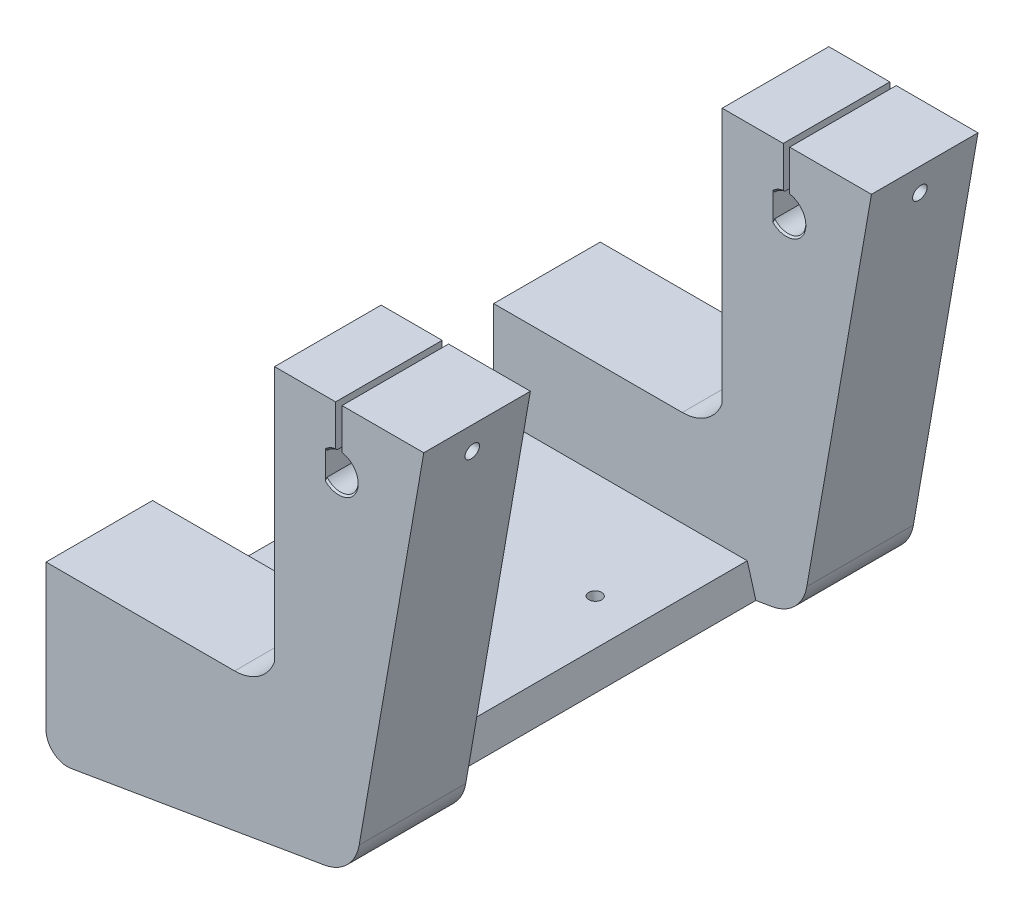
SolidWorks part; units mm, degrees
material "PLA"
ref_plane "Front Plane" through (0, 0, 0) normal (0, 0, 1) x (1, 0, 0)
ref_plane "Top Plane" through (0, 0, 0) normal (0, 1, 0) x (1, 0, 0)
ref_plane "Right Plane" through (0, 0, 0) normal (1, 0, 0) x (0, 0, -1)
sketch "Sketch1" plane through (0, 0, 0) normal (0, 0, 1) x (1, 0, 0)
  line L1 (0, 0) -> (0, -25.5549)
  line L2 (0, 0) -> (0, 36) construction
  line L3 (0, 36) -> (-73.6122, -6.5) construction
  line L4 (-73.6122, -6.5) -> (-73.6122, -40.5794)
  line L5 (-67.7751, -45.5088) -> (-8.3259, -35.4138)
  line L6 (-73.6122, -6.5) -> (-29.3679, -6.5)
  line L7 (-19.971, 0.0798) -> (-20, 0)
  line L8 (-20, 0) -> (0, 0)
  arc A0 (0, -25.5549) -> (-8.3259, -35.4138) centre (-10, -25.5549) cw
  arc A1 (-29.3679, -6.5) -> (-19.971, 0.0798) centre (-29.3679, 3.5) ccw
  arc A2 (-67.7751, -45.5088) -> (-73.6122, -40.5794) centre (-68.6122, -40.5794) cw
  point P10 (0, -34)
  point P15 (-73.6122, -46.5)
  dimension "D8" = 10
  dimension "D9" = 10
  dimension "D10" = 5
  dimension "D1" = 36
  dimension "D2" = 70
  dimension "D3" = 60
  dimension "D4" = 40
  dimension "D5" = 85
  dimension "D6" = 110
  dimension "D7" = 20
extrude "Boss-Extrude1" add sketch "Sketch1" along normal mid plane 130
sketch "Sketch2" plane through (0, 0, 0) normal (0, 0, 1) x (1, 0, 0)
  line L0 (-20, 0) -> (-19.971, 0.0798) construction
  line L1 (0, -25.5549) -> (0, 0) construction
  line L2 (0, 0) -> (-20, 0) construction
  line L3 (-20, 0) -> (-19.971, 0.0798)
  line L4 (0, -25.5549) -> (0, 0)
  line L5 (0, 0) -> (-20, 0)
  line L6 (-21.617, -2.8185) -> (-12.1021, -36.055)
  line L7 (-67.7751, -45.5088) -> (-8.3259, -35.4138) construction
  line L8 (-12.1021, -36.055) -> (-8.3259, -35.4138)
  arc A0 (-29.3679, -6.5) -> (-19.971, 0.0798) centre (-29.3679, 3.5) ccw construction
  arc A1 (-8.3259, -35.4138) -> (0, -25.5549) centre (-10, -25.5549) ccw construction
  arc A2 (-21.617, -2.8185) -> (-19.971, 0.0798) centre (-29.3679, 3.5) ccw
  arc A3 (-8.3259, -35.4138) -> (0, -25.5549) centre (-10, -25.5549) ccw
extrude "Cut-Extrude1" cut sketch "Sketch2" against normal mid plane 80
sketch "Sketch5" plane through (0, -6.5, 0) normal (0, 1, 0) x (1, 0, 0)
  line L0 (-73.6122, -65) -> (-73.6122, 65) construction
  line L1 (-73.6122, 40) -> (-29.4017, 40)
  line L2 (-73.6122, 40) -> (-73.6122, -40)
  line L3 (-73.6122, -40) -> (-29.3679, -40)
  line L5 (-29.3679, -65) -> (-29.3679, 65) construction
  line L6 (-29.3679, 65) -> (-73.6122, 65) construction
  line L7 (-29.3679, -65) -> (-73.6122, -65) construction
  line L8 (-29.3679, -40) -> (0, -40)
  line L9 (0, -40) -> (0, 40)
  line L10 (0, 40) -> (-29.4017, 40)
  dimension "D1" = 25
  dimension "D2" = 25
extrude "Cut-Extrude4" cut sketch "Sketch5" against normal mid plane 45
sketch "Sketch11" plane through (0, 0, 0) normal (0, 1, 0) x (1, 0, 0)
  line L4 (0, 40) -> (0, 65)
  line L5 (0, 65) -> (-20, 65)
  line L6 (0, 40) -> (0, 65)
  line L7 (-20, 40) -> (0, 40)
  line L9 (0, 65) -> (-20, 65)
  line L11 (-20, 40) -> (0, 40)
  line L12 (0, -65) -> (0, -40)
  line L13 (0, -40) -> (-20, -40)
  line L14 (0, -65) -> (0, -40)
  line L15 (-20, -65) -> (0, -65)
  line L17 (0, -40) -> (-20, -40)
  line L19 (-20, -65) -> (0, -65)
  line L20 (-20, 65) -> (-20, 40)
  line L21 (-20, 65) -> (-20, 40)
  line L22 (-20, -40) -> (-20, -65)
  line L23 (-20, -40) -> (-20, -65)
  dimension "D1" = 0
  dimension "D2" = 0
extrude "Boss-Extrude2" add sketch "Sketch11" along normal blind 10
sketch "Sketch21" plane through (0, -29, 0) normal (0, 1, 0) x (1, 0, 0)
  spline S0 degree 3 poles (-21.5583, 19.7378) (-22.8487, 27.9291) (-25.5661, 32.3034) (-29.3541, 33.8932) (-33.4476, 33.1215) (-37.5645, 29.7634) (-44.5046, 28.9554) (-50.5909, 24.7684) (-57.9898, 24.025) (-63.3265, 17.9503) (-67.9952, 12.8299) (-69.0209, 5.7814) (-70.1103, -1.5411) (-68.1224, -13.7152) (-56.3757, -25.6869) (-41.6282, -27.1568) (-32.2243, -35.9995) (-21.8917, -31.4552) (-21.3427, -20.9224) (-28.6879, -18.8427) (-35.8576, -19.9446) (-42.9657, -16.2552) (-51.1482, -15.2115) (-59.5064, -12.216) (-60.6235, -2.532) (-62.203, 7.4336) (-54.5699, 15.0358) (-46.1033, 16.1741) (-38.5301, 18.2527) (-31.0416, 18.6638) (-21.5583, 19.7378) (-22.8487, 27.9291) (-25.5661, 32.3034) knots -0.094127 -0.058473 -0.027989 0 0.022726 0.035577 0.0479 0.072394 0.099349 0.131513 0.162299 0.185923 0.228841 0.244701 0.272897 0.320837 0.392238 0.460867 0.49926 0.537584 0.573008 0.596702 0.619844 0.663291 0.689274 0.724829 0.7599 0.799837 0.846558 0.871867 0.905873 0.941527 0.972011 1 1.022726 1.035577 1.0479 only from (-23.3472, 27.9647) to (-23.3472, 27.9647)
extrude "Boss-Extrude4" [suppressed] add sketch "Sketch21" along normal blind 8 draft 8
sketch "Sketch24" plane through (0, 0, -65) normal (0, 0, -1) x (-1, 0, 0)
  line L0 (0.1473, -27.2651) -> (-15, 60)
  line L1 (-15, 60) -> (20, 60)
  line L2 (20, 60) -> (20, 0.001)
  line L3 (20, 10) -> (20, 0.001) construction
  line L4 (0.1473, -27.2651) -> (20, 0.001)
  line L5 (0, 10) -> (20, 10) construction
  arc A0 (0, -25.5549) -> (8.3259, -35.4138) centre (10, -25.5549) ccw construction
  dimension "D1" = 50
  dimension "D2" = 35
extrude "Boss-Extrude6" add sketch "Sketch24" against normal up to surface (25 mm away) up to face at (-24.8322, -15.1011, -40)
sketch "Sketch25" plane through (0, 0, 65) normal (0, 0, 1) x (1, 0, 0)
  line L0 (-0.1473, -27.2651) -> (-20, 0.001) construction
  line L1 (15, 60) -> (-20, 60) construction
  line L2 (-20, 60) -> (-20, 0.001) construction
  line L3 (-0.1473, -27.2651) -> (15, 60) construction
  line L4 (-0.1473, -27.2651) -> (-20, 0.001)
  line L5 (15, 60) -> (-20, 60)
  line L6 (-20, 60) -> (-20, 0.001)
  line L7 (-0.1473, -27.2651) -> (15, 60)
extrude "Boss-Extrude7" add sketch "Sketch25" against normal up to surface (25 mm away) up to face at (-24.8322, -15.1011, 40)
sketch "Sketch26" plane through (0, 0, -65) normal (0, 0, -1) x (-1, 0, 0)
  line L0 (2.5, 60) -> (4.9301, 46) construction
  line L1 (20, 60) -> (-15, 60) construction
  line L2 (-15, 60) -> (0.1473, -27.2651) construction
  line L3 (4.9301, 46) -> (4.9301, 60) construction
  line L6 (4.1801, 50.0817) -> (4.1801, 61.2175)
  line L7 (4.1801, 61.2175) -> (5.6801, 61.2175)
  line L8 (5.6801, 50.0817) -> (5.6801, 61.2175)
  arc A0 (4.1801, 50.0817) -> (5.6801, 50.0817) centre (4.9301, 46) ccw
  point P13 (4.9301, 61.2175)
  dimension "D2" = 8.3
  dimension "D1" = 14
  dimension "D3" = 1.5
extrude "Cut-Extrude16" cut sketch "Sketch26" against normal up to surface (130 mm away) contours A0 L8 L7 L6 up to face at (-30.7414, -5.0985, 65)
sketch "Sketch27" plane through (-20, 0, 0) normal (-1, 0, 0) x (0, 0, 1)
  line L0 (-52.5, 60) -> (-52.5, 53.5) construction
  line L1 (-40, 60) -> (-65, 60) construction
  line L2 (-52.5, 53.5) -> (52.5, 60) construction
  line L3 (40, 60) -> (65, 60) construction
  line L4 (52.5, 60) -> (52.5, 53.5) construction
  circle A0 centre (-52.5, 53.5) radius 1.5
  circle A1 centre (52.5, 53.5) radius 1.5
  dimension "D1" = 3
  dimension "D2" = 6.5
extrude "Cut-Extrude17" cut sketch "Sketch27" against normal blind 50
sketch "Sketch28" plane through (-4.1801, 0, 0) normal (-1, 0, 0) x (0, 0, 1)
  circle A2 centre (52.5, 53.5) radius 1.7
  circle A3 centre (52.5, 53.5) radius 1.7
  circle A6 centre (-52.5, 53.5) radius 1.7
  circle A7 centre (-52.5, 53.5) radius 1.7
  dimension "D1" = 0.2
  dimension "D2" = 0.2
extrude "Cut-Extrude18" cut sketch "Sketch28" against normal blind 50
sketch "Sketch29" plane through (0, 0, 65) normal (0, 0, 1) x (1, 0, 0)
  line L0 (-4.9301, 41.85) -> (-4.9301, 46) construction
  line L2 (-4.9301, 46) -> (-9.0801, 46) construction
  line L3 (-8.0801, 43.2981) -> (-8.0801, 48.7019)
  arc A0 (-5.6801, 50.0817) -> (-4.1801, 50.0817) centre (-4.9301, 46) ccw construction
  arc A1 (-8.0801, 48.7019) -> (-8.0801, 43.2981) centre (-4.9301, 46) ccw
  point P10 (-8.0801, 46)
  dimension "D1" = 1
extrude "Boss-Extrude8" add sketch "Sketch29" against normal up to surface (25 mm away) up to face at (-18.1213, 11.3881, 40)
sketch "Sketch30" plane through (0, 0, -40) normal (0, 0, 1) x (1, 0, 0)
  line L2 (-8.0801, 48.7019) -> (-8.0801, 43.2981)
  arc A0 (-8.0801, 48.7019) -> (-8.0801, 43.2981) centre (-4.9301, 46) ccw construction
  arc A1 (-8.0801, 48.7019) -> (-8.0801, 43.2981) centre (-4.9301, 46) ccw
extrude "Boss-Extrude9" add sketch "Sketch30" against normal up to surface (25 mm away) up to face at (-22.7995, 12.7727, -65)
chamfer "Chamfer9" distance 0.4 angle 45 12 edges at (-6.9985, 49.5978, 40) (-1.3323, 43.9316, 40) (-1.3323, 43.9316, -40) (-6.9985, 49.5978, -40) (-1.3323, 43.9316, -65) (-6.9985, 49.5978, -65) (-1.3323, 43.9316, 65) (-6.9985, 49.5978, 65) (-4.1801, 51.8, -52.5) (-4.1801, 51.8, 52.5) (-20, 53.5, 54) (-20, 53.5, -51)
sketch "Sketch31" plane through (5.6117, -33.0471, 0) normal (0.1674, -0.9859, 0) x (0.9859, 0.1674, 0)
  line L0 (-74.4373, 65) -> (-14.1371, 65) construction
  line L1 (-59.2872, -15) -> (-29.2872, -15) construction
  line L2 (-59.2872, -15) -> (-59.2872, 15) construction
  line L3 (-59.2872, 15) -> (-29.2872, 15) construction
  line L4 (-29.2872, -15) -> (-29.2872, 15) construction
  line L5 (-59.2872, -15) -> (-29.2872, 15) construction
  line L6 (-59.2872, 15) -> (-29.2872, -15) construction
  circle A0 centre (-29.2872, 15) radius 1.5
  circle A1 centre (-29.2872, -15) radius 1.5
  circle A2 centre (-59.2872, -15) radius 1.5
  circle A3 centre (-59.2872, 15) radius 1.5
  point P0 (-44.2872, 0)
  point P10 (-44.2872, 65)
  point P19 (-44.2872, 0)
  dimension "D3" = 3
  dimension "D1" = 30
  dimension "D2" = 30
  dimension "D4" = 4
extrude "Cut-Extrude19" cut sketch "Sketch31" against normal blind 10
fillet "Fillet1" radius 0.2 4 edges at (-51.36, -42.7214, 15) (-51.36, -42.7214, -15) (-21.7834, -37.699, -15) (-21.7834, -37.699, 15)
